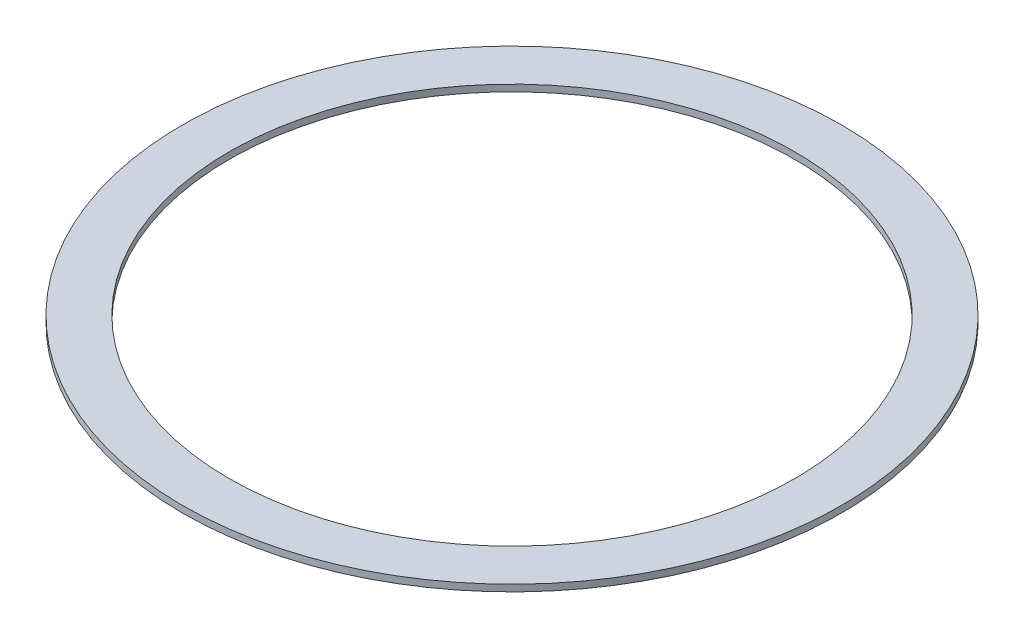
SolidWorks part; units mm, degrees
ref_plane "Plano frontal" through (0, 0, 0) normal (0, 0, 1) x (1, 0, 0)
ref_plane "Plano superior" through (0, 0, 0) normal (0, 1, 0) x (1, 0, 0)
ref_plane "Plano direito" through (0, 0, 0) normal (1, 0, 0) x (0, 0, -1)
sketch "Esboço1" plane through (0, 0, 0) normal (0, 1, 0) x (1, 0, 0)
  circle A0 centre (0, 0) radius 99
  circle A1 centre (0, 0) radius 85
  dimension "D1" = 198
  dimension "D2" = 170
extrude "Ressalto-extrusão1" add sketch "Esboço1" along normal blind 2
